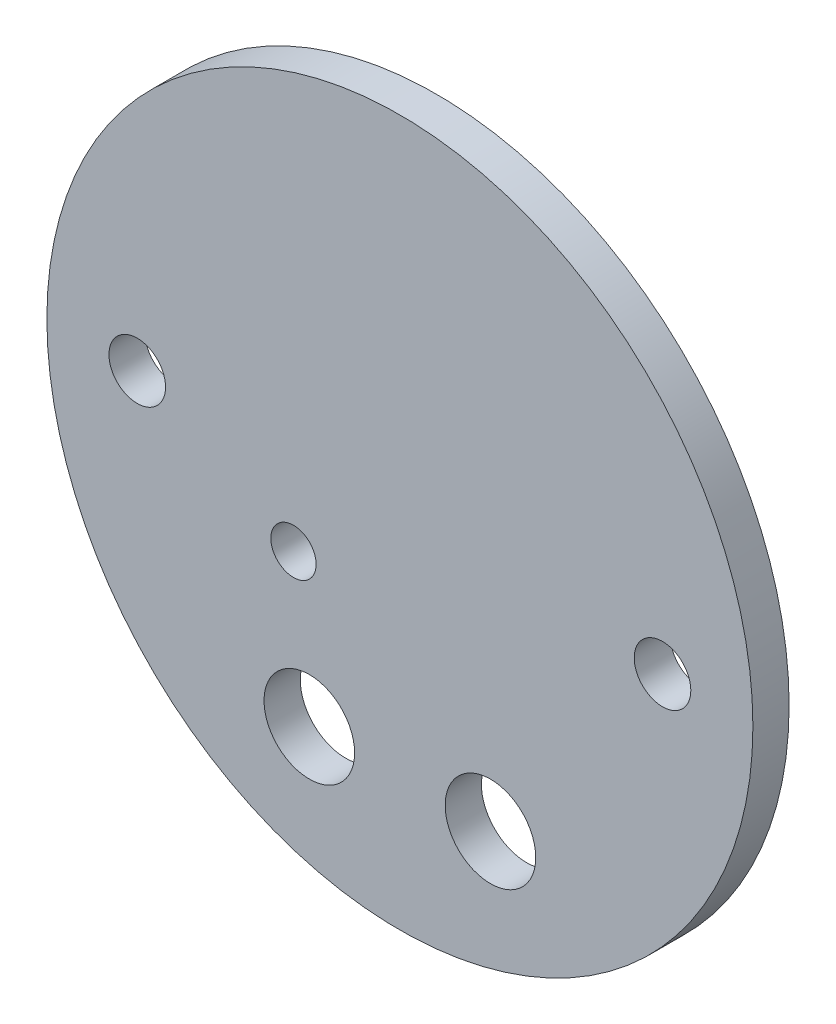
SolidWorks part; units mm, degrees
ref_plane "Front Plane" through (0, 0, 0) normal (0, 0, 1) x (1, 0, 0)
ref_plane "Top Plane" through (0, 0, 0) normal (0, 1, 0) x (1, 0, 0)
ref_plane "Right Plane" through (0, 0, 0) normal (1, 0, 0) x (0, 0, -1)
sketch "Sketch1" plane through (0, 0, 0) normal (0, 0, 1) x (1, 0, 0)
  circle A0 centre (0, 0) radius 49.5046
  dimension "D1" = 99.0092
extrude "Boss-Extrude1" add sketch "Sketch1" along normal blind 5.08
sketch "Sketch2" plane through (0, 0, 5.08) normal (0, 0, 1) x (1, 0, 0)
  circle A0 centre (0, 0) radius 47.625
  dimension "D1" = 95.25
extrude "Boss-Extrude2" add sketch "Sketch2" along normal blind 3.175
sketch "Sketch3" plane through (0, 0, 8.255) normal (0, 0, 1) x (1, 0, 0)
  circle A0 centre (-12.7, -31.1668) radius 6.35
  circle A1 centre (12.7, -31.1668) radius 6.35
  circle A2 centre (-12.7, -31.1668) radius 12.7 construction
  circle A3 centre (12.7, -31.1668) radius 12.7 construction
  circle A4 centre (12.7, -31.1668) radius 13.97 construction
  circle A5 centre (-12.7, -31.1668) radius 13.97 construction
  circle A6 centre (0, 0) radius 47.625 construction
  circle A7 centre (-36.83, 0) radius 3.9687
  circle A8 centre (36.83, 0) radius 3.9687
  circle A9 centre (0, 6.35) radius 15.24 construction
  circle A10 centre (-14.9213, -10.9686) radius 8.89 construction
  circle A11 centre (0, 6.35) radius 16.51 construction
  circle A12 centre (-14.9213, -10.9686) radius 7.62 construction
  circle A14 centre (-14.9213, -10.9686) radius 3.175
  dimension "D1" = 12.7
  dimension "D2" = 12.7
  dimension "D3" = 27.94
  dimension "D4" = 27.94
  dimension "D5" = 25.4
  dimension "D6" = 25.4
  dimension "D7" = 7.9375
  dimension "D8" = 7.9375
  dimension "D11" = 30.48
  dimension "D12" = 33.02
  dimension "D13" = 15.24
  dimension "D14" = 17.78
  dimension "D16" = 6.35
  dimension "D9" = 73.66
  dimension "2.9/2" = 36.83
  dimension "D17" = 6.35
extrude "Cut-Extrude1" cut sketch "Sketch3" against normal through all
sketch "Sketch4" plane through (0, 0, 8.255) normal (0, 0, 1) x (1, 0, 0)
  circle A0 centre (0, 0) radius 53.6578
extrude "Cut-Extrude2" cut sketch "Sketch4" against normal blind 3.175
